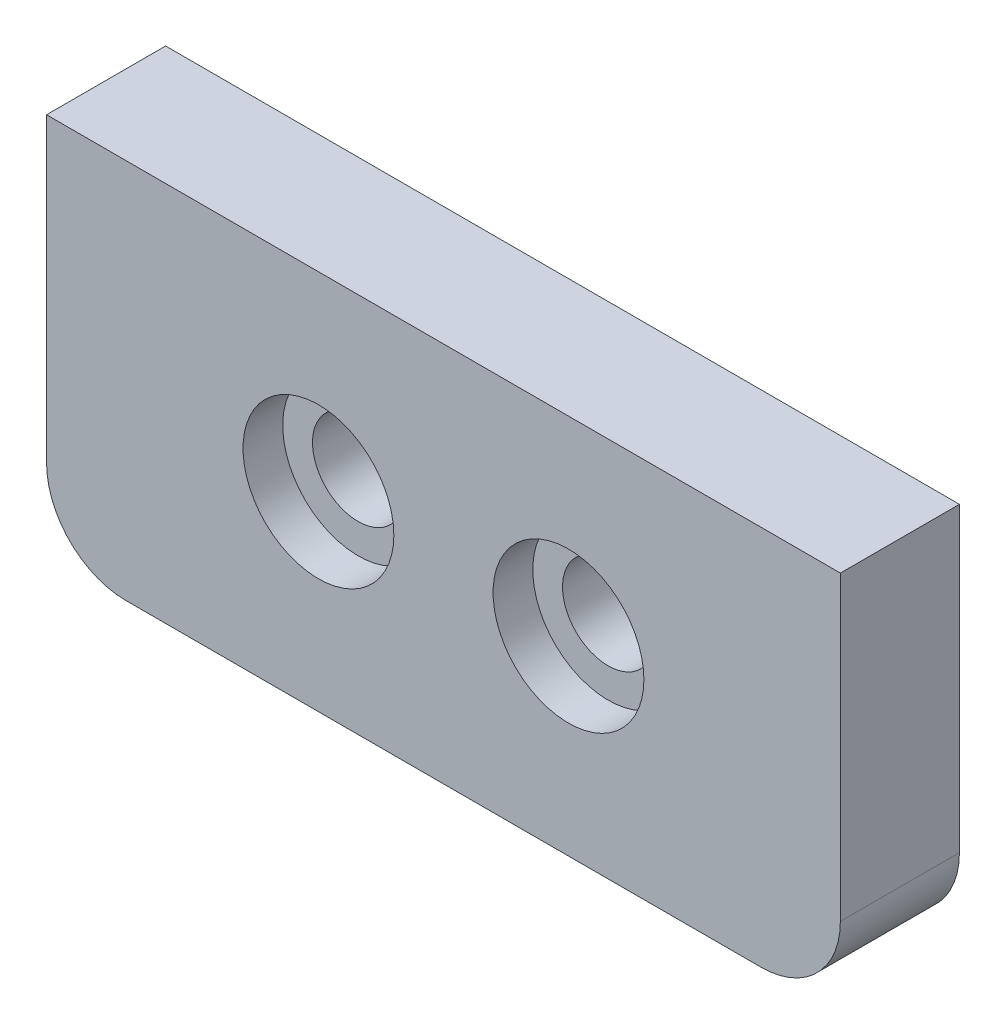
SolidWorks part; units mm, degrees
ref_plane "Front Plane" through (0, 0, 0) normal (0, 0, 1) x (1, 0, 0)
ref_plane "Top Plane" through (0, 0, 0) normal (0, 1, 0) x (1, 0, 0)
ref_plane "Right Plane" through (0, 0, 0) normal (1, 0, 0) x (0, 0, -1)
sketch "Sketch1" plane through (0, 0, 0) normal (0, 0, 1) x (1, 0, 0)
  line L0 (0, 4.8) -> (20, 4.8) construction
  line L1 (0, 0) -> (20, 0)
  line L2 (0, 0) -> (0, 9.6)
  line L3 (0, 9.6) -> (20, 9.6)
  line L4 (20, 0) -> (20, 9.6)
  line L5 (10, 9.6) -> (10, 0) construction
  circle A0 centre (6.85, 4.8) radius 1.15
  circle A1 centre (13.15, 4.8) radius 1.15
  dimension "D3" = 2.3
  dimension "D1" = 20
  dimension "D2" = 9.6
  dimension "D4" = 3.15
  dimension "D5" = 6.3
extrude "Boss-Extrude1" add sketch "Sketch1" along normal blind 3
fillet "Fillet1" radius 2 2 edges at (0, 0, 1.5) (20, 0, 1.5)
sketch "Sketch2" plane through (0, 0, 3) normal (0, 0, 1) x (1, 0, 0)
  circle A0 centre (6.85, 4.8) radius 1.9
  circle A1 centre (13.15, 4.8) radius 1.9
  dimension "D1" = 3.8
extrude "Cut-Extrude1" cut sketch "Sketch2" against normal blind 1
